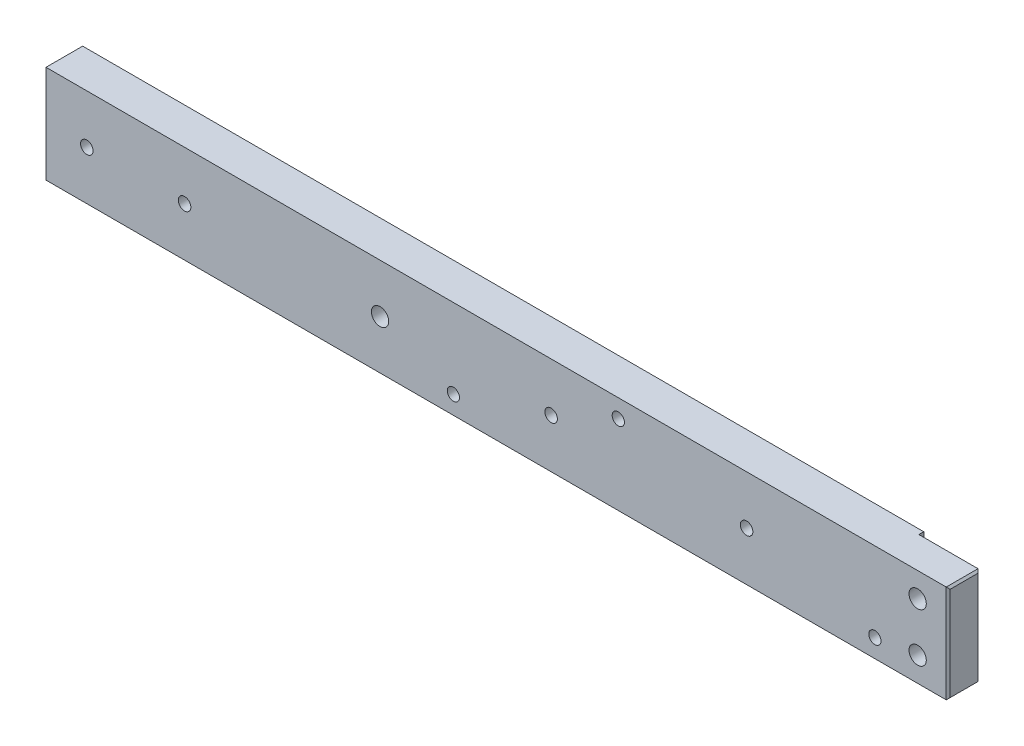
SolidWorks part; units mm, degrees
material "6061-T6 (SS)"
ref_plane "Front Plane" through (0, 0, 0) normal (0, 0, 1) x (1, 0, 0)
ref_plane "Top Plane" through (0, 0, 0) normal (0, 1, 0) x (1, 0, 0)
ref_plane "Right Plane" through (0, 0, 0) normal (1, 0, 0) x (0, 0, -1)
sketch "Sketch1" plane through (0, 0, 0) normal (0, 0, 1) x (1, 0, 0)
  line L1 (0, 0) -> (-234.95, 0)
  line L2 (0, 0) -> (0, 25.4)
  line L3 (0, 25.4) -> (-234.95, 25.4)
  line L4 (-234.95, 0) -> (-234.95, 25.4)
  dimension "D1" = 25.4
  dimension "D2" = 234.95
extrude "Boss-Extrude1" add sketch "Sketch1" along normal blind 9.525
sketch "Sketch2" plane through (0, 0, 9.525) normal (0, 0, 1) x (1, 0, 0)
  line L0 (-7.9375, 6.35) -> (-7.9375, 19.05)
  line L1 (-7.9375, 19.05) -> (-7.9375, 25.4)
  line L2 (0, 25.4) -> (-234.95, 25.4) construction
  line L3 (-7.9375, 6.35) -> (-7.9375, 0)
  line L4 (-234.95, 0) -> (0, 0) construction
  line L5 (0, 0) -> (0, 25.4) construction
  dimension "D1" = 7.9375
  dimension "D2" = 12.7
hole_wizard "#8 Clearance Hole1" positions "Sketch3" profile "Sketch4" hole size "#8" standard "ANSI Inch"
sketch "Sketch3" plane through (0, 0, 9.525) normal (0, 0, 1) x (1, 0, 0)
  point P0 (-7.9375, 6.35)
  point P3 (-7.9375, 19.05)
sketch "Sketch4" plane through (-7.9375, 6.35, 9.525) normal (1, 0, 0) x (0, -1, 0)
  line L0 (0, 0) -> (0, 26.7507)
  line L1 (0, 26.7507) -> (2.2479, 25.4)
  line L2 (2.2479, 25.4) -> (2.2479, 0)
  line L5 (2.2479, 0) -> (0, 0)
  line L10 (0, 26.7507) -> (-2.2479, 25.4) construction
  line L11 (0, -6.35) -> (0, 107.95) construction
  dimension "Hole Dia." = 4.4958
  dimension "Hole Depth" = 25.4
  dimension "Drill Angle" = 118
hole_wizard "#8 Clearance Hole2" positions "Sketch8" profile "Sketch9" hole size "#8" standard "ANSI Inch"
sketch "Sketch8" plane through (0, 0, 9.525) normal (0, 0, 1) x (1, 0, 0)
  line L0 (-211.1375, 12.7) -> (-147.6375, 12.7)
  line L1 (-211.1375, 12.7) -> (-234.95, 12.7)
  line L2 (-234.95, 25.4) -> (-234.95, 0) construction
  point P2 (-147.6375, 12.7)
  dimension "D1" = 63.5
  dimension "D2" = 23.8125
sketch "Sketch9" plane through (-147.6375, 12.7, 9.525) normal (1, 0, 0) x (0, -1, 0)
  line L0 (0, 0) -> (0, 20.4007)
  line L1 (0, 20.4007) -> (2.2479, 19.05)
  line L2 (2.2479, 19.05) -> (2.2479, 0)
  line L5 (2.2479, 0) -> (0, 0)
  line L10 (0, 20.4007) -> (-2.2479, 19.05) construction
  line L11 (0, -6.35) -> (0, 107.95) construction
  dimension "Hole Dia." = 4.4958
  dimension "Hole Depth" = 19.05
  dimension "Drill Angle" = 118
hole_wizard "#4 Clearance Hole3" positions "Sketch10" profile "Sketch12" hole size "#4" standard "ANSI Inch" end condition through all
sketch "Sketch10" plane through (0, 0, 0) normal (0, 0, -1) x (-1, 0, 0)
  line L0 (103.1875, 12.7) -> (52.3875, 12.7)
  line L2 (52.3875, 12.7) -> (52.3875, 25.4) construction
  line L3 (0, 25.4) -> (234.95, 25.4) construction
  line L5 (52.3875, 12.7) -> (52.3875, 0) construction
  line L7 (234.95, 25.4) -> (234.95, 0) construction
  circle A1 centre (52.3875, 12.7) radius 1.1303
  circle A3 centre (103.1875, 12.7) radius 1.1303
  point P0 (103.1875, 12.7)
  point P3 (52.3875, 12.7)
  point P28 (52.3875, 12.7)
  point P29 (48.9074, 25.4)
  point P30 (49.5727, 25.4)
  point P31 (100.3727, 12.7)
  dimension "D1" = 50.8
  dimension "D2" = 131.7625
sketch "Sketch12" plane through (-103.1875, 12.7, 0) normal (1, 0, 0) x (0, 1, 0)
  line L0 (0, 0) -> (0, 9.525)
  line L1 (0, 9.525) -> (1.6319, 9.525)
  line L2 (1.6319, 9.525) -> (1.6319, 0)
  line L5 (1.6319, 0) -> (0, 0)
  line L11 (0, -6.35) -> (0, 107.95) construction
  dimension "Thru Hole Dia." = 3.2639
  dimension "Thru Hole Depth" = 9.525
hole_wizard "#4 Clearance Hole2" positions "Sketch13" profile "Sketch14" hole size "#4" standard "ANSI Inch" end condition up to next
sketch "Sketch13" plane through (0, 0, 9.525) normal (0, 0, 1) x (1, 0, 0)
  line L0 (-223.8375, 12.7) -> (-198.4375, 12.7)
  line L3 (-147.6375, 12.7) -> (-211.1375, 12.7) construction
  point P0 (-223.8375, 12.7)
  point P2 (-198.4375, 12.7)
  dimension "D1" = 25.4
  dimension "D2" = 63.5
sketch "Sketch14" plane through (-223.8375, 12.7, 9.525) normal (1, 0, 0) x (0, -1, 0)
  line L0 (0, 0) -> (0, 9.525)
  line L1 (0, 9.525) -> (1.6319, 9.525)
  line L2 (1.6319, 9.525) -> (1.6319, 0)
  line L5 (1.6319, 0) -> (0, 0)
  line L11 (0, -6.35) -> (0, 107.95) construction
  dimension "Thru Hole Dia." = 3.2639
  dimension "Thru Hole Depth" = 9.525
hole_wizard "1/8 (0.125) Diameter Hole1" positions "Sketch15" profile "Sketch17" hole size "1/8" standard "ANSI Inch" end condition up to next
sketch "Sketch15" plane through (0, 0, 9.525) normal (0, 0, 1) x (1, 0, 0)
  line L2 (-85.725, 20.6375) -> (-19.05, 4.7625)
  line L6 (-234.95, 0) -> (0, 0) construction
  line L7 (-234.95, 0) -> (0, 0) construction
  line L8 (0, 25.4) -> (-234.95, 25.4) construction
  line L11 (0, 0) -> (0, 25.4) construction
  line L12 (-133.0325, 0) -> (-133.0325, 25.4) construction
  point P0 (-19.05, 4.7625)
  point P2 (-85.725, 20.6375)
  point P22 (-128.5875, 4.7625)
  dimension "D1" = 66.675
  dimension "D2" = 19.05
  dimension "D3" = 4.7625
  dimension "D4" = 4.7625
  dimension "D5" = 4.445
  dimension "D6" = 4.7625
sketch "Sketch17" plane through (-19.05, 4.7625, 9.525) normal (1, 0, 0) x (0, -1, 0)
  line L0 (0, 0) -> (0, 9.525)
  line L1 (0, 9.525) -> (1.5875, 9.525)
  line L2 (1.5875, 9.525) -> (1.5875, 0)
  line L5 (1.5875, 0) -> (0, 0)
  line L11 (0, -6.35) -> (0, 107.95) construction
  dimension "Thru Hole Dia." = 3.175
  dimension "Thru Hole Depth" = 9.525
sketch "Sketch18" plane through (0, 0, 0) normal (0, 0, -1) x (-1, 0, 0)
  line L0 (0, 25.4) -> (234.95, 25.4) construction
  line L1 (0, 0) -> (15.875, 0)
  line L2 (0, 0) -> (0, 25.4)
  line L3 (0, 25.4) -> (15.875, 25.4)
  line L4 (15.875, 0) -> (15.875, 25.4)
  circle A0 centre (7.9375, 6.35) radius 2.2479 construction
  circle A1 centre (7.9375, 6.35) radius 2.2479
  dimension "D1" = 7.9375
extrude "Cut-Extrude1" cut sketch "Sketch18" against normal blind 1.27
chamfer "Chamfer1" distance 0.508 angle 45 8 edges at (-234.95, 25.4, 4.7625) (-234.95, 12.7, 9.525) (-234.95, 0, 4.7625) (-234.95, 12.7, 0) (0, 12.7, 9.525) (0, 25.4, 5.3975) (0, 12.7, 1.27) (0, 0, 5.3975)
